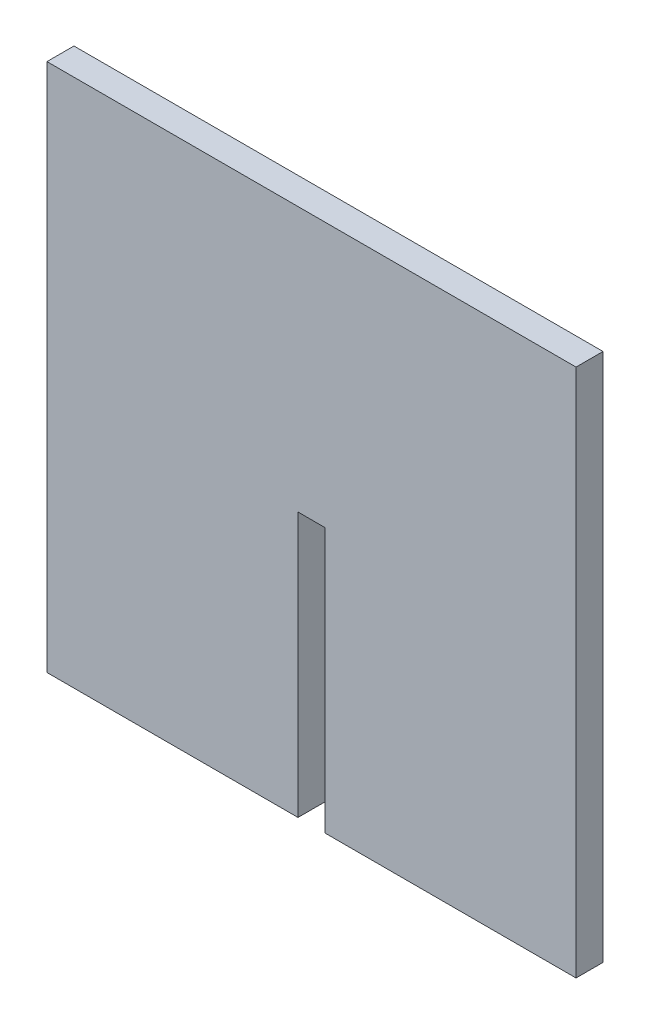
SolidWorks part; units mm, degrees
material "Balsa"
ref_plane "Front Plane" through (0, 0, 0) normal (0, 0, 1) x (1, 0, 0)
ref_plane "Top Plane" through (0, 0, 0) normal (0, 1, 0) x (1, 0, 0)
ref_plane "Right Plane" through (0, 0, 0) normal (1, 0, 0) x (0, 0, -1)
sketch "Sketch1" plane through (0, 0, 0) normal (0, 0, 1) x (1, 0, 0)
  line L0 (40.141, 21.15) -> (0, 21.15) construction
  line L1 (0, 0) -> (40.141, 0)
  line L2 (0, 0) -> (0, 84.6)
  line L3 (0, 84.6) -> (84.6, 84.6)
  line L4 (84.6, 0) -> (84.6, 84.6)
  line L6 (40.141, 0) -> (40.141, 42.3)
  line L7 (40.141, 42.3) -> (44.459, 42.3)
  line L8 (44.459, 0) -> (44.459, 42.3)
  line L9 (44.459, 0) -> (84.6, 0)
  line L10 (44.459, 21.15) -> (84.6, 21.15) construction
  dimension "D1" = 84.6
  dimension "D2" = 84.6
  dimension "D3" = 42.3
  dimension "D4" = 4.318
extrude "Boss-Extrude1" add sketch "Sketch1" along normal blind 4.318
